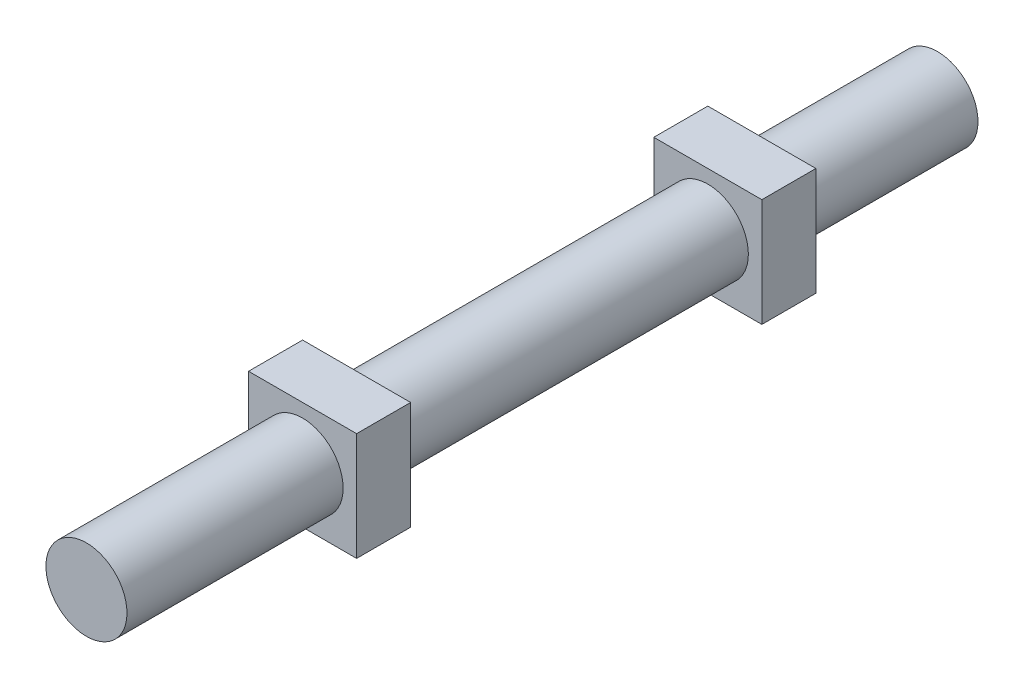
SolidWorks part; units mm, degrees
material "Ductile Iron"
ref_plane "Front Plane" through (0, 0, 0) normal (0, 0, 1) x (1, 0, 0)
ref_plane "Top Plane" through (0, 0, 0) normal (0, 1, 0) x (1, 0, 0)
ref_plane "Right Plane" through (0, 0, 0) normal (1, 0, 0) x (0, 0, -1)
sketch "Sketch1" plane through (0, 0, 0) normal (0, 0, 1) x (1, 0, 0)
  circle A0 centre (0, 0) radius 7.5
  dimension "D1" = 15
extrude "Boss-Extrude1" add sketch "Sketch1" along normal blind 157.5
ref_plane "Plane1" through (0, 0, 107.5) normal (0, 0, 1) x (1, 0, 0)
ref_plane "Plane2" through (0, 0, 32.5) normal (0, 0, 1) x (1, 0, 0)
sketch "Sketch2" plane through (0, 0, 107.5) normal (0, 0, 1) x (1, 0, 0)
  line L1 (-10, 10) -> (10, 10)
  line L2 (-10, 10) -> (-10, -10)
  line L3 (-10, -10) -> (10, -10)
  line L4 (10, 10) -> (10, -10)
  line L5 (-10, 10) -> (10, -10) construction
  line L6 (-10, -10) -> (10, 10) construction
  point P0 (0, 0)
  dimension "D1" = 20
  dimension "D2" = 20
extrude "Boss-Extrude2" add sketch "Sketch2" along normal blind 10
sketch "Sketch3" plane through (0, 0, 32.5) normal (0, 0, 1) x (1, 0, 0)
  line L1 (-10, 10) -> (10, 10)
  line L2 (-10, 10) -> (-10, -10)
  line L3 (-10, -10) -> (10, -10)
  line L4 (10, 10) -> (10, -10)
  line L5 (-10, 10) -> (10, -10) construction
  line L6 (-10, -10) -> (10, 10) construction
  point P0 (0, 0)
extrude "Boss-Extrude3" add sketch "Sketch3" along normal blind 10
